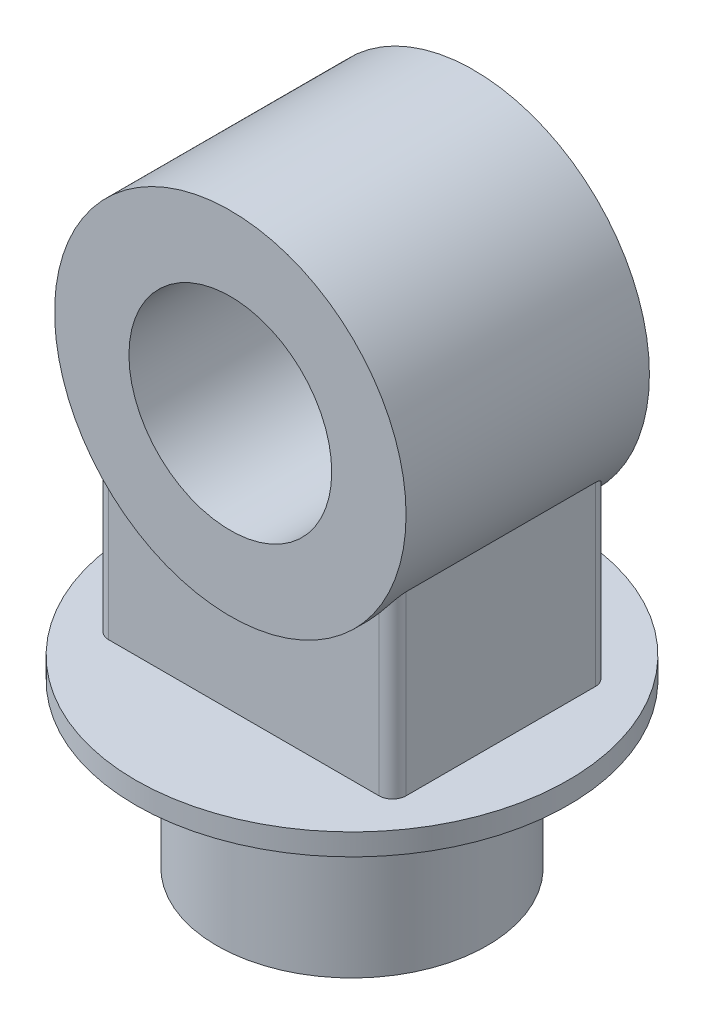
SolidWorks part; units mm, degrees
ref_plane "Front Plane" through (0, 0, 0) normal (0, 0, 1) x (1, 0, 0)
ref_plane "Top Plane" through (0, 0, 0) normal (0, 1, 0) x (1, 0, 0)
ref_plane "Right Plane" through (0, 0, 0) normal (1, 0, 0) x (0, 0, -1)
sketch "Sketch2" plane through (0, 0, 0) normal (0, 1, 0) x (1, 0, 0)
  circle A0 centre (0, 0) radius 100
  dimension "D1" = 200
extrude "Boss-Extrude1" add sketch "Sketch2" along normal blind 120
sketch "Sketch3" plane through (0, 120, 0) normal (0, 1, 0) x (1, 0, 0)
  circle A0 centre (0, 0) radius 160
  dimension "D1" = 320
extrude "Boss-Extrude2" add sketch "Sketch3" along normal blind 16
sketch "Sketch4" plane through (0, 0, 0) normal (0, 0, 1) x (1, 0, 0)
  line L0 (160, 136) -> (-160, 136) construction
  circle A0 centre (0, 336) radius 75
  circle A1 centre (0, 336) radius 130
  point P5 (0, 0)
  dimension "D1" = 260
  dimension "D2" = 150
  dimension "D3" = 200
extrude "Boss-Extrude7" add sketch "Sketch4" along normal mid plane 180 separate body
sketch "Sketch6" plane through (0, 136, 0) normal (0, 1, 0) x (1, 0, 0)
  line L1 (-110, 80) -> (110, 80)
  line L2 (-110, 80) -> (-110, -80)
  line L3 (-110, -80) -> (110, -80)
  line L4 (110, 80) -> (110, -80)
  line L5 (-110, 80) -> (110, -80) construction
  line L6 (-110, -80) -> (110, 80) construction
  point P0 (0, 0)
  dimension "D1" = 160
  dimension "D2" = 220
extrude "Boss-Extrude8" add sketch "Sketch6" along normal up to next
fillet "Fillet1" radius 10 4 edges at (-110, 201.359, -80) (110, 201.359, -80) (110, 201.359, 80) (-110, 201.359, 80)
